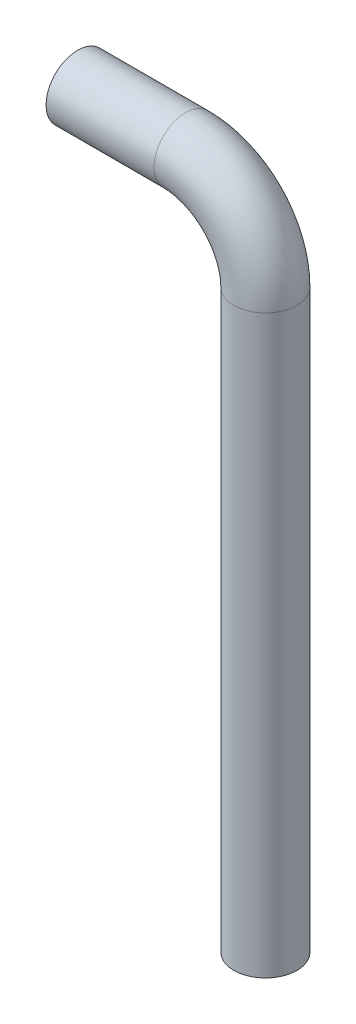
SolidWorks part; units mm, degrees
ref_plane "Front Plane" through (0, 0, 0) normal (0, 0, 1) x (1, 0, 0)
ref_plane "Top Plane" through (0, 0, 0) normal (0, 1, 0) x (1, 0, 0)
ref_plane "Right Plane" through (0, 0, 0) normal (1, 0, 0) x (0, 0, -1)
sketch "Sketch4" plane through (0, 0, 0) normal (0, 0, 1) x (1, 0, 0)
  line L0 (30.9782, 0) -> (-30.9782, 0) construction
  arc A0 (56.324, 0) -> (0, 56.324) centre (0, 0) ccw
sketch "Sketch5" plane through (0, 0, 0) normal (0, 1, 0) x (1, 0, 0)
  circle A0 centre (56.324, 0) radius 19.05
  circle A1 centre (56.324, 0) radius 22.225
  dimension "D1" = 38.1
  dimension "D2" = 44.45
sweep "Sweep1" add profiles "Sketch5" path "Sketch4"
sketch "Sketch6" plane through (0, 0, 0) normal (-1, 0, 0) x (0, 0, 1)
  circle A0 centre (0, 56.324) radius 19.05
  circle A1 centre (0, 56.324) radius 22.225
  circle A2 centre (0, 56.324) radius 22.225
  dimension "D1" = 0
extrude "Boss-Extrude1" add sketch "Sketch6" along normal blind 76.2
sketch "Sketch7" plane through (0, 0, 0) normal (0, -1, 0) x (1, 0, 0)
  circle A0 centre (56.324, 0) radius 19.05
  circle A1 centre (56.324, 0) radius 22.225
  circle A2 centre (56.324, 0) radius 22.225
  dimension "D1" = 0
extrude "Boss-Extrude2" add sketch "Sketch7" along normal blind 406.4
